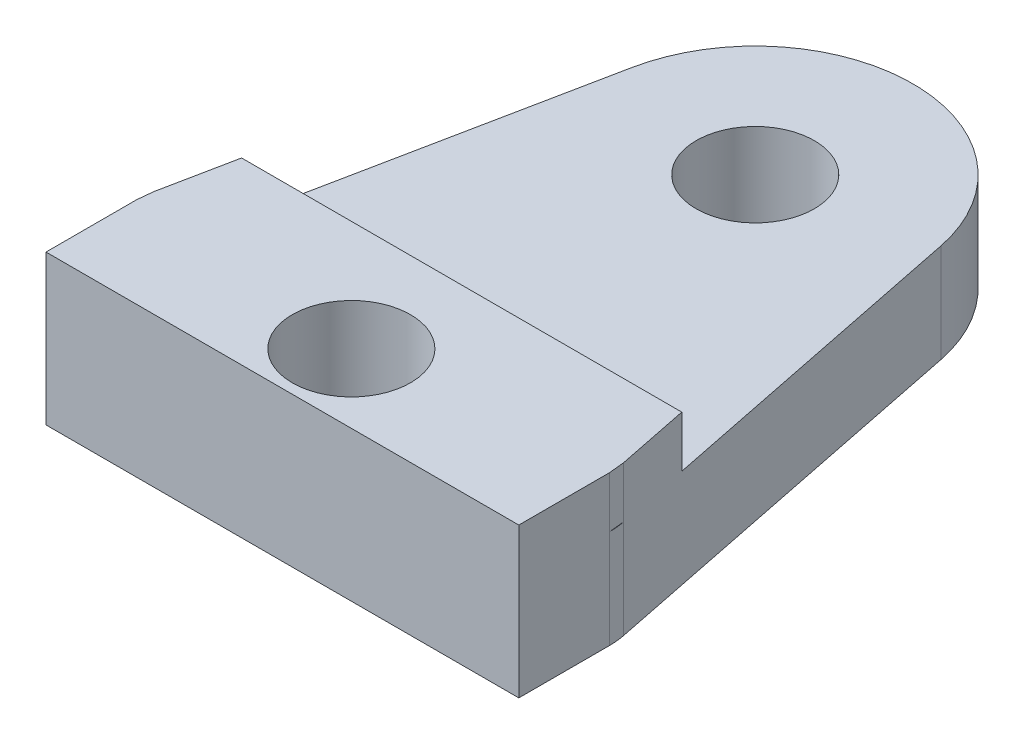
SolidWorks part; units mm, degrees
ref_plane "Front Plane" through (0, 0, 0) normal (0, 0, 1) x (1, 0, 0)
ref_plane "Top Plane" through (0, 0, 0) normal (0, 1, 0) x (1, 0, 0)
ref_plane "Right Plane" through (0, 0, 0) normal (1, 0, 0) x (0, 0, -1)
sketch "Sketch1" plane through (0, 0, 0) normal (0, 1, 0) x (1, 0, 0)
  line L0 (2.0792, 12.7921) -> (0, 2.5)
  line L1 (0, 0) -> (12, 0)
  line L2 (0, 0) -> (0, 2.5)
  line L4 (12, 0) -> (12, 2.5)
  line L5 (12, 2.5) -> (9.9208, 12.7921)
  arc A0 (9.9208, 12.7921) -> (2.0792, 12.7921) centre (6, 12) ccw
  circle A1 centre (6, 12) radius 1.5
  dimension "D7" = 3
  dimension "D4" = 8
  dimension "D1" = 12
  dimension "D2" = 12
  dimension "D3" = 6
  dimension "D5" = 2.5
  dimension "D6" = 2.5
extrude "Boss-Extrude1" add sketch "Sketch1" along normal blind 2.5
fillet "Fillet2" radius 2 2 edges at (0, 1.25, -2.5) (12, 1.25, -2.5)
sketch "Sketch2" plane through (0, 2.5, 0) normal (0, 1, 0) x (1, 0, 0)
  line L0 (0.4141, 4.55) -> (11.5859, 4.55)
  line L3 (2.0792, 12.7921) -> (0.0396, 2.696) construction
  line L4 (11.9604, 2.696) -> (9.9208, 12.7921) construction
  line L5 (0, 0) -> (12, 0) construction
  line L6 (0.4141, 4.55) -> (0.0396, 2.696)
  line L7 (0.0396, 2.696) -> (0, 2.3)
  line L8 (0, 2.3) -> (0, 0)
  line L9 (0, 0) -> (12, 0)
  line L10 (12, 0) -> (12, 2.3)
  line L11 (12, 2.3) -> (11.9604, 2.696)
  line L12 (11.9604, 2.696) -> (11.5859, 4.55)
  dimension "D1" = 4.55
extrude "Boss-Extrude2" add sketch "Sketch2" along normal blind 1.3
sketch "Sketch3" plane through (0, 3.8, 0) normal (0, 1, 0) x (1, 0, 0)
  line L0 (0, 0) -> (12, 0) construction
  circle A0 centre (6, 1.75) radius 1.5
  dimension "D1" = 3
  dimension "D2" = 6
  dimension "D3" = 1.75
extrude "Cut-Extrude1" cut sketch "Sketch3" against normal up to surface (3.8 mm away) up to face at (6, 0, -4.8483)
